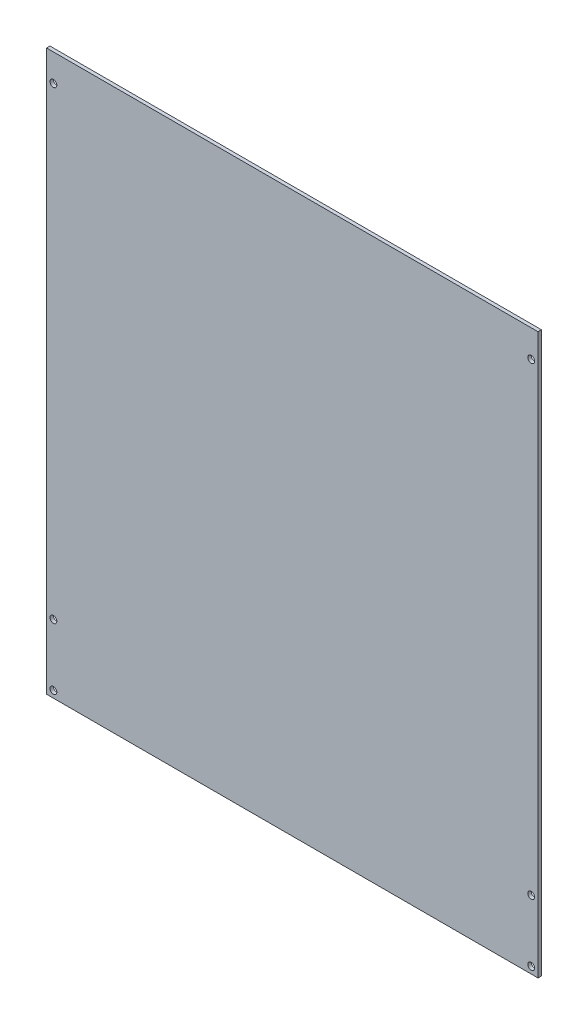
SolidWorks part; units mm, degrees
material "PC High Viscosity"
ref_plane "Front Plane" through (0, 0, 0) normal (0, 0, 1) x (1, 0, 0)
ref_plane "Top Plane" through (0, 0, 0) normal (0, 1, 0) x (1, 0, 0)
ref_plane "Right Plane" through (0, 0, 0) normal (1, 0, 0) x (0, 0, -1)
sketch "Sketch1" plane through (0, 0, 0) normal (0, 0, 1) x (1, 0, 0)
  line L1 (-228.6, -260.35) -> (228.6, -260.35)
  line L2 (-228.6, -260.35) -> (-228.6, 260.35)
  line L3 (-228.6, 260.35) -> (228.6, 260.35)
  line L4 (228.6, -260.35) -> (228.6, 260.35)
  line L5 (-228.6, -260.35) -> (228.6, 260.35) construction
  line L6 (-228.6, 260.35) -> (228.6, -260.35) construction
  point P0 (0, 0)
  dimension "D1" = 520.7
  dimension "D2" = 457.2
extrude "Boss-Extrude1" add sketch "Sketch1" along normal blind 3.175
sketch "Sketch2" plane through (0, 0, 3.175) normal (0, 0, 1) x (1, 0, 0)
  line L0 (228.6, -260.35) -> (228.6, 260.35) construction
  line L1 (-228.6, -260.35) -> (228.6, -260.35) construction
  line L2 (-228.6, 260.35) -> (-228.6, -260.35) construction
  line L3 (228.6, 260.35) -> (-228.6, 260.35) construction
  circle A0 centre (-222.25, 234.95) radius 3.175
  circle A1 centre (222.25, 234.95) radius 3.175
  circle A2 centre (-222.25, -254) radius 3.175
  circle A3 centre (222.25, -254) radius 3.175
  circle A4 centre (-222.25, -196.85) radius 3.175
  circle A7 centre (222.25, -196.85) radius 3.175
  dimension "D3" = 6.35
  dimension "D6" = 6.35
  dimension "D9" = 6.35
  dimension "D12" = 6.35
  dimension "D14" = 6.35
  dimension "D1" = 6.35
  dimension "D2" = 6.35
  dimension "D4" = 6.35
  dimension "D5" = 6.35
  dimension "D7" = 25.4
  dimension "D8" = 6.35
  dimension "D11" = 6.35
  dimension "D13" = 57.15
extrude "Cut-Extrude1" cut sketch "Sketch2" against normal blind 3.175
